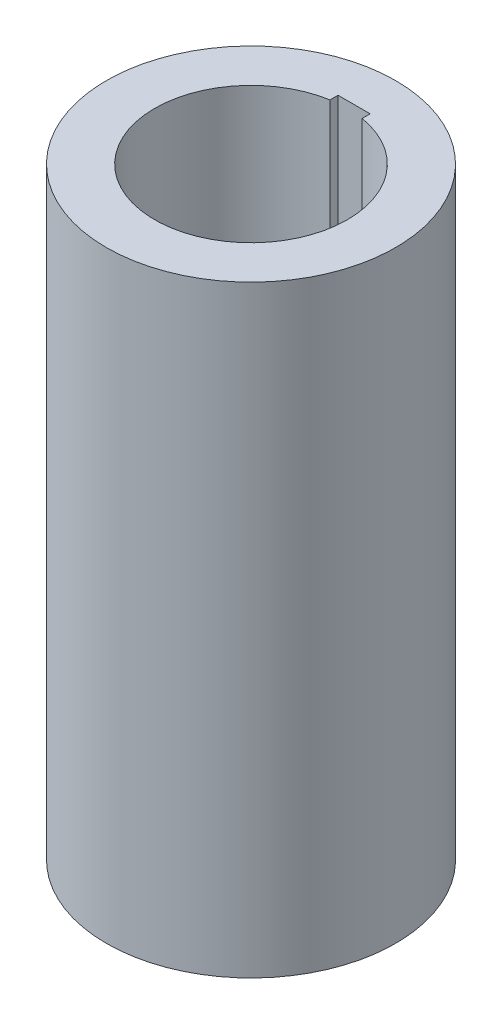
SolidWorks part; units mm, degrees
ref_plane "Front Plane" through (0, 0, 0) normal (0, 0, 1) x (1, 0, 0)
ref_plane "Top Plane" through (0, 0, 0) normal (0, 1, 0) x (1, 0, 0)
ref_plane "Right Plane" through (0, 0, 0) normal (1, 0, 0) x (0, 0, -1)
sketch "Sketch1" plane through (0, 0, 0) normal (0, 1, 0) x (1, 0, 0)
  line L0 (0, 0) -> (0, 18) construction
  line L1 (-2, 12.8322) -> (2, 12.8322)
  line L2 (2, 12.8322) -> (2, 11.8322)
  line L3 (-2, 12.8322) -> (-2, 11.8322)
  circle A0 centre (0, 0) radius 12
  circle A1 centre (0, 0) radius 18
  point P8 (0, 12.8322)
  dimension "D1" = 24
  dimension "D2" = 36
  dimension "D3" = 4
  dimension "D4" = 1
extrude "Boss-Extrude1" add sketch "Sketch1" along normal blind 75
